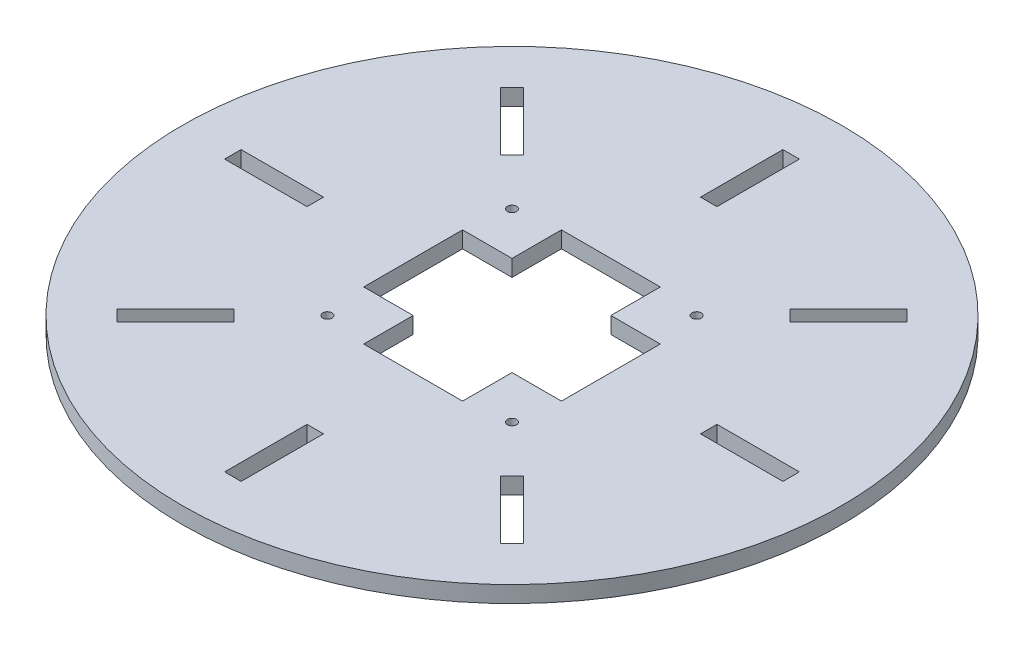
SolidWorks part; units mm, degrees
ref_plane "前视基准面" through (0, 0, 0) normal (0, 0, 1) x (1, 0, 0)
ref_plane "上视基准面" through (0, 0, 0) normal (0, 1, 0) x (1, 0, 0)
ref_plane "右视基准面" through (0, 0, 0) normal (1, 0, 0) x (0, 0, -1)
sketch "草图1" plane through (0, 0, 0) normal (0, 1, 0) x (1, 0, 0)
  circle A0 centre (0, 0) radius 100
  dimension "D1" = 200
extrude "凸台-拉伸1" add sketch "草图1" along normal blind 5
sketch "草图2" plane through (0, 5, 0) normal (0, 1, 0) x (1, 0, 0)
  circle A0 centre (28, 28) radius 1.4
  circle A4 centre (28, -28) radius 1.4
  circle A5 centre (-28, -28) radius 1.4
  circle A6 centre (-28, 28) radius 1.4
  point P12 (0, 0)
  dimension "D1" = 2.8
  dimension "D2" = 28
  dimension "D3" = 28
  dimension "D4" = 4
extrude "切除-拉伸1" cut sketch "草图2" against normal blind 5
sketch "草图3" plane through (0, 5, 0) normal (0, 1, 0) x (1, 0, 0)
  line L1 (30.3505, 24.7124) -> (32.0224, 28.3917)
  line L2 (32.0224, 28.3917) -> (29.672, 31.6794)
  line L3 (29.672, 31.6794) -> (25.6495, 31.2876)
  line L4 (25.6495, 31.2876) -> (23.9776, 27.6083)
  line L5 (23.9776, 27.6083) -> (26.328, 24.3206)
  line L6 (26.328, 24.3206) -> (30.3505, 24.7124)
  circle A0 centre (28, 28) radius 3.5 construction
  circle A1 centre (28, 28) radius 1.5
  dimension "D2" = 3
  dimension "D1" = 3.5
sketch "草图4" plane through (0, 5, 0) normal (0, 1, 0) x (1, 0, 0)
  line L0 (0, 67.1195) -> (0, -66.3732) construction
  line L1 (-42.0053, 0) -> (37.8491, 0) construction
  line L2 (-2.5, 59.7) -> (2.5, 59.7)
  line L3 (-2.5, 59.7) -> (-2.5, 84.7)
  line L4 (-2.5, 84.7) -> (2.5, 84.7)
  line L5 (2.5, 59.7) -> (2.5, 84.7)
  line L6 (-2.5, 59.7) -> (2.5, 84.7) construction
  line L7 (-2.5, 84.7) -> (2.5, 59.7) construction
  line L8 (2.5, -59.7) -> (-2.5, -59.7)
  line L9 (2.5, -59.7) -> (2.5, -84.7)
  line L10 (2.5, -84.7) -> (-2.5, -84.7)
  line L11 (-2.5, -59.7) -> (-2.5, -84.7)
  line L12 (2.5, -59.7) -> (-2.5, -84.7) construction
  line L13 (2.5, -84.7) -> (-2.5, -59.7) construction
  point P3 (0, 72.2)
  point P8 (0, -72.2)
  point P15 (0, 59.7)
  point P16 (0, -59.7)
  dimension "D1" = 119.4
  dimension "D2" = 5
  dimension "D3" = 5
  dimension "D4" = 25
  dimension "D5" = 25
extrude "切除-拉伸2" cut sketch "草图4" against normal up to next (5 mm away)
pattern_circular "阵列(圆周)2" count 4 every 45 about axis through (0, 0, 0) along (0, 1, 0) of "切除-拉伸2"
sketch "草图5" plane through (0, 5, 0) normal (0, 1, 0) x (1, 0, 0)
  line L1 (-30, -15) -> (30, -15)
  line L2 (-30, -15) -> (-30, 15)
  line L3 (-30, 15) -> (30, 15)
  line L4 (30, -15) -> (30, 15)
  line L5 (-30, -15) -> (30, 15) construction
  line L6 (-30, 15) -> (30, -15) construction
  line L7 (-15, -30) -> (15, -30)
  line L8 (-15, -30) -> (-15, 30)
  line L9 (-15, 30) -> (15, 30)
  line L10 (15, -30) -> (15, 30)
  line L11 (-15, -30) -> (15, 30) construction
  line L12 (-15, 30) -> (15, -30) construction
  point P0 (0, 0)
  point P5 (0, 0)
  dimension "D1" = 60
  dimension "D2" = 30
  dimension "D3" = 30
  dimension "D4" = 60
extrude "切除-拉伸3" cut sketch "草图5" against normal blind 5 contours L1 L10 L3 L8 | L3 L10 L9 L8 | L10 L1 L4 L3 | L7 L10 L1 L8 | L1 L8 L3 L2
